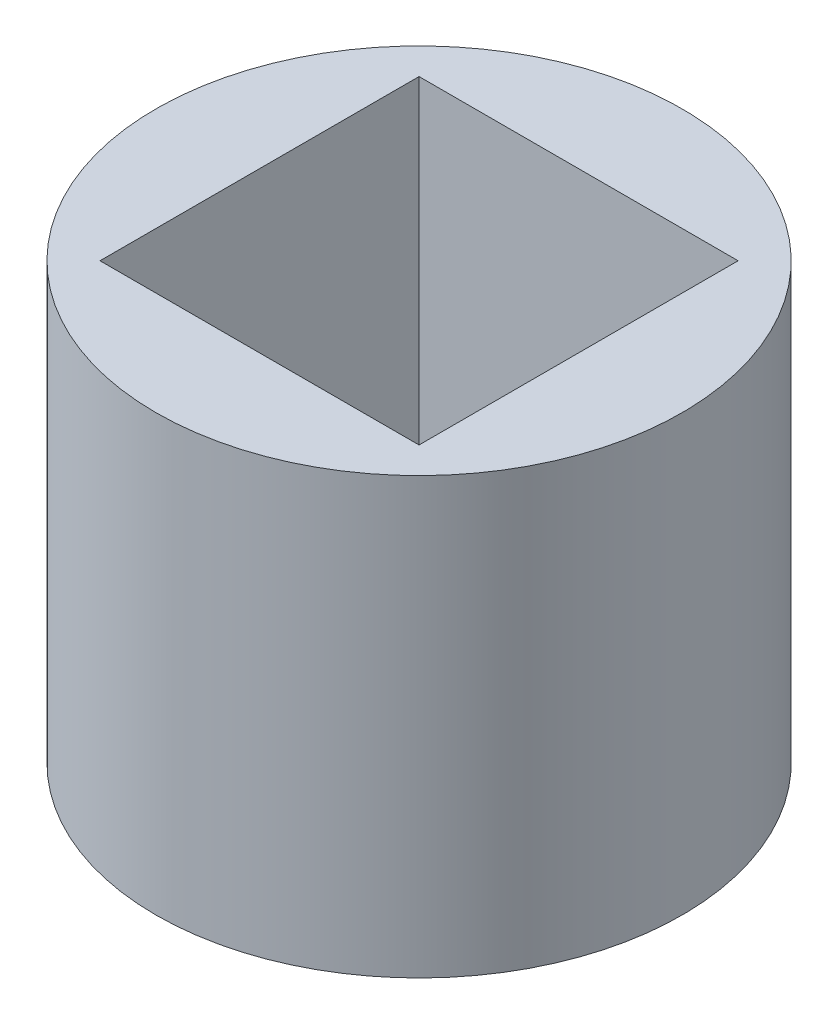
SolidWorks part; units mm, degrees
ref_plane "Front Plane" through (0, 0, 0) normal (0, 0, 1) x (1, 0, 0)
ref_plane "Top Plane" through (0, 0, 0) normal (0, 1, 0) x (1, 0, 0)
ref_plane "Right Plane" through (0, 0, 0) normal (1, 0, 0) x (0, 0, -1)
sketch "Sketch2" plane through (0, 0, 0) normal (0, 1, 0) x (1, 0, 0)
  line L1 (-7.7, 7.7) -> (7.7, 7.7)
  line L2 (-7.7, 7.7) -> (-7.7, -7.7)
  line L3 (-7.7, -7.7) -> (7.7, -7.7)
  line L4 (7.7, 7.7) -> (7.7, -7.7)
  line L5 (-7.7, 7.7) -> (7.7, -7.7) construction
  line L6 (-7.7, -7.7) -> (7.7, 7.7) construction
  circle A0 centre (0, 0) radius 12.7
extrude "Boss-Extrude2" add sketch "Sketch2" along normal blind 21 contours A0
